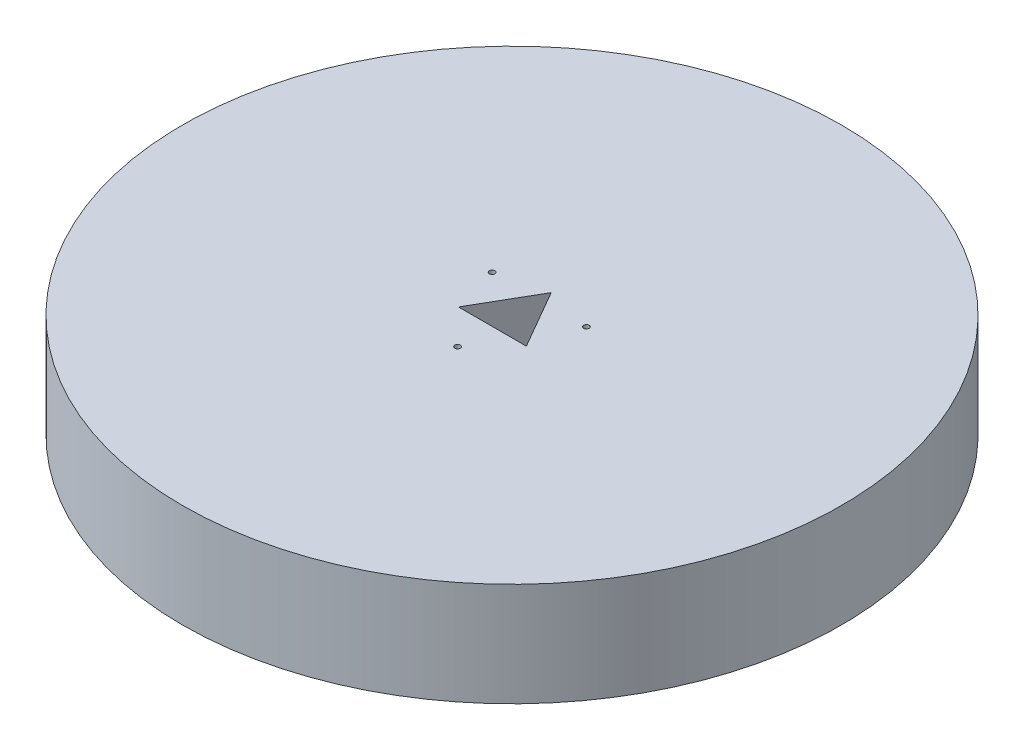
SolidWorks part; units mm, degrees
ref_plane "Front Plane" through (0, 0, 0) normal (0, 0, 1) x (1, 0, 0)
ref_plane "Top Plane" through (0, 0, 0) normal (0, 1, 0) x (1, 0, 0)
ref_plane "Right Plane" through (0, 0, 0) normal (1, 0, 0) x (0, 0, -1)
sketch "Sketch1" plane through (0, 0, 0) normal (0, 1, 0) x (1, 0, 0)
  circle A0 centre (0, 0) radius 60.5
  dimension "D1" = 121
extrude "Boss-Extrude1" add sketch "Sketch1" along normal blind 19
sketch "Sketch2" plane through (0, 19, 0) normal (0, 1, 0) x (1, 0, 0)
  line L0 (0, 14.3784) -> (0, -15.0721) construction
  line L1 (-14.5373, 8.3931) -> (0, 0) construction
  line L2 (0, 0) -> (12.3294, -7.1184) construction
  line L3 (10.7981, 6.2343) -> (0, 0) construction
  line L4 (0, 0) -> (-14.1466, -8.1675) construction
  line L5 (0, 7.2) -> (6.2354, -3.6)
  line L6 (6.2354, -3.6) -> (-6.2354, -3.6)
  line L7 (-6.2354, -3.6) -> (0, 7.2)
  circle A0 centre (-8.6603, 5) radius 0.5
  circle A1 centre (8.6603, 5) radius 0.5
  circle A2 centre (0, -10) radius 0.5
  point P19 (0, 0)
  dimension "D1" = 10
  dimension "D6" = 1
  dimension "D2" = 120
  dimension "D3" = 120
  dimension "D4" = 7.2
  dimension "D5" = 7.2
  dimension "D7" = 3
extrude "Cut-Extrude2" cut sketch "Sketch2" against normal through all
